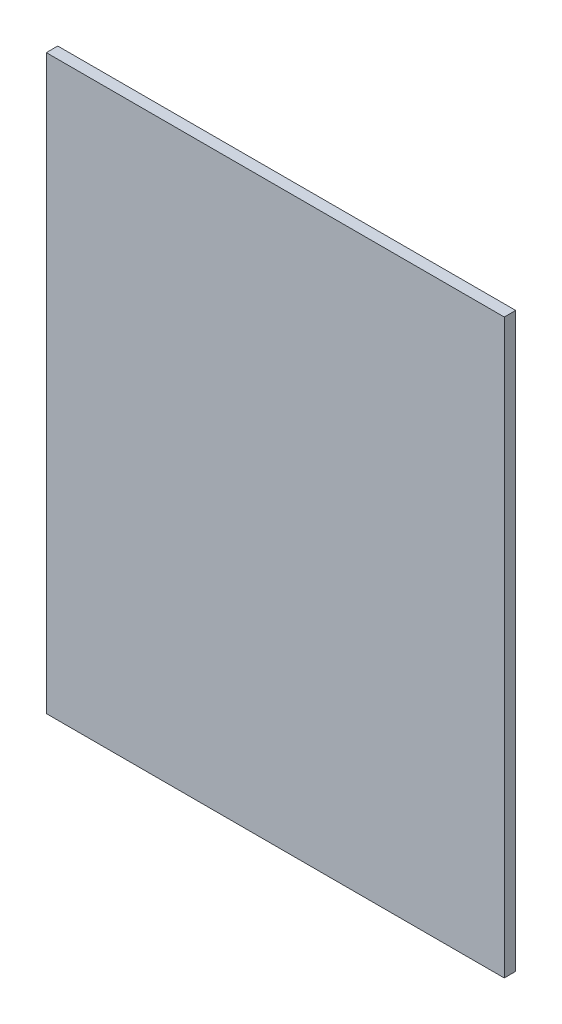
SolidWorks part; units mm, degrees
ref_plane "Front Plane" through (0, 0, 0) normal (0, 0, 1) x (1, 0, 0)
ref_plane "Top Plane" through (0, 0, 0) normal (0, 1, 0) x (1, 0, 0)
ref_plane "Right Plane" through (0, 0, 0) normal (1, 0, 0) x (0, 0, -1)
sketch "Sketch1" plane through (0, 0, 0) normal (0, 0, 1) x (1, 0, 0)
  line L1 (0, 0) -> (120, 0)
  line L2 (0, 0) -> (0, 150)
  line L3 (0, 150) -> (120, 150)
  line L4 (120, 0) -> (120, 150)
  dimension "D1" = 150
  dimension "D2" = 120
extrude "Boss-Extrude1" add sketch "Sketch1" along normal blind 3
